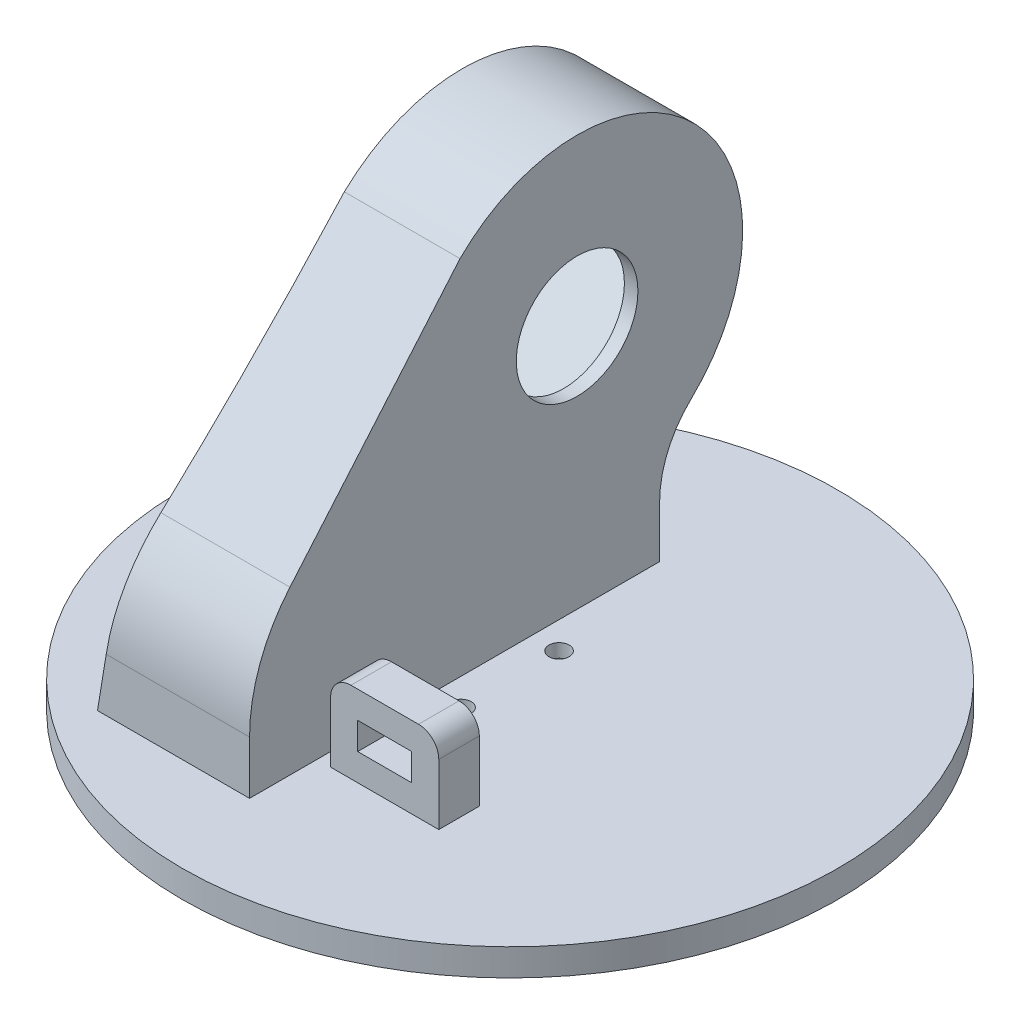
SolidWorks part; units mm, degrees
ref_plane "Front Plane" through (0, 0, 0) normal (0, 0, 1) x (1, 0, 0)
ref_plane "Top Plane" through (0, 0, 0) normal (0, 1, 0) x (1, 0, 0)
ref_plane "Right Plane" through (0, 0, 0) normal (1, 0, 0) x (0, 0, -1)
sketch "Sketch2" plane through (0, 0, 0) normal (0, 1, 0) x (1, 0, 0)
  circle A0 centre (0, 0) radius 48.5
  dimension "D1" = 97
extrude "Boss-Extrude1" add sketch "Sketch2" along normal blind 4
sketch "Sketch4" plane through (0, 0, 0) normal (0, -1, 0) x (1, 0, 0)
  circle A0 centre (0, 7.25) radius 1.5
  circle A1 centre (0, -7.25) radius 1.5
  dimension "D1" = 3
  dimension "D2" = 3
  dimension "D3" = 14.5
  dimension "D4" = 7.25
extrude "Cut-Extrude2" cut sketch "Sketch4" against normal through all
sketch "Sketch5" plane through (0, 0, 0) normal (0, -1, 0) x (1, 0, 0)
  circle A0 centre (0, 0) radius 3.75
  dimension "D1" = 7.5
extrude "Cut-Extrude3" cut sketch "Sketch5" against normal blind 1.5
ref_plane "Plane1" through (-4, 0, 0) normal (1, 0, 0) x (0, 0, -1)
sketch "Sketch7" plane through (-4, 0, 0) normal (1, 0, 0) x (0, 0, -1)
  line L0 (23.1299, 11.6445) -> (23.1299, 4)
  line L5 (48.5, 4) -> (-48.5, 4) construction
  line L6 (-27.2273, 29.5362) -> (-1.2843, 55.4793)
  line L7 (-43.5609, 4) -> (23.1299, 4)
  line L11 (-34.5496, 4) -> (-34.5496, 11.8586)
  arc A4 (28.7298, 24.692) -> (-1.2843, 55.4793) centre (13.9185, 40.2765) ccw
  arc A5 (28.7298, 24.692) -> (23.1299, 11.6445) centre (41.1299, 11.6445) ccw
  arc A6 (-27.2273, 29.5362) -> (-34.5496, 11.8586) centre (-9.5496, 11.8586) ccw
  dimension "D1" = 25
  dimension "D4" = 43
  dimension "D3" = 18
  dimension "D5" = 45
extrude "Boss-Extrude2" add sketch "Sketch7" against normal blind 14
ref_plane "Plane2" through (-6, 0, 0) normal (1, 0, 0) x (0, 0, -1)
sketch "Sketch8" plane through (-6, 0, 0) normal (1, 0, 0) x (0, 0, -1)
  line L0 (-27.2273, 29.5362) -> (-1.2843, 55.4793) construction
  line L1 (-15.2496, 25.9576) -> (13.7417, 54.9489)
  line L2 (-15.2496, 25.9576) -> (-0.4004, 11.1083)
  line L3 (-0.4004, 11.1083) -> (28.591, 40.0997)
  line L4 (13.7417, 54.9489) -> (28.591, 40.0997)
  line L5 (-15.2496, 25.9576) -> (28.591, 40.0997) construction
  line L6 (-0.4004, 11.1083) -> (13.7417, 54.9489) construction
  point P0 (6.6707, 33.0286)
  point P11 (13.9185, 40.2765)
  dimension "D1" = 41
  dimension "D2" = 21
  dimension "D3" = 90
  dimension "D4" = 20.5
  dimension "D5" = 90
  dimension "D6" = 10.25
  dimension "D7" = 10.5
extrude "Cut-Extrude5" cut sketch "Sketch8" against normal up to next
sketch "Sketch9" plane through (-18, 0, 0) normal (-1, 0, 0) x (0, 0, 1)
  line L0 (-13.7417, 54.9489) -> (-28.591, 40.0997) construction
  line L3 (-21.1664, 47.5243) -> (-22.536, 48.894) construction
  circle A0 centre (-20.1057, 53.5347) radius 1.3
  circle A1 centre (-27.1768, 46.4637) radius 1.3
  circle A2 centre (6.7644, 12.5225) radius 1.3
  circle A3 centre (13.8354, 19.5936) radius 1.3
  dimension "D1" = 2.6
  dimension "D5" = 5
  dimension "D6" = 90
  dimension "D2" = 3.5
  dimension "D3" = 2
  dimension "D4" = 2
extrude "Cut-Extrude6" cut sketch "Sketch9" against normal blind 7.5
sketch "Sketch11" plane through (-4, 0, 0) normal (1, 0, 0) x (0, 0, -1)
  circle A0 centre (13.9185, 40.2765) radius 9
  dimension "D1" = 18
extrude "Cut-Extrude9" cut sketch "Sketch11" against normal up to next
sketch "Sketch17" plane through (-18, 0, 0) normal (-1, 0, 0) x (0, 0, 1)
  line L0 (29.3486, 31.6576) -> (3.4056, 57.6006)
  line L1 (-26.1299, 11.6445) -> (-26.1299, 1)
  line L2 (-26.1299, 1) -> (37.5496, 1)
  line L3 (37.5496, 1) -> (37.5496, 11.8586)
  line L4 (27.2273, 29.5362) -> (1.2843, 55.4793)
  line L5 (-23.1299, 11.6445) -> (-23.1299, 4)
  line L6 (-23.1299, 4) -> (34.5496, 4)
  line L7 (34.5496, 4) -> (34.5496, 11.8586)
  line L9 (-23.1299, 11.6445) -> (-23.1299, 4)
  line L10 (-23.1299, 4) -> (34.5496, 4)
  line L11 (34.5496, 4) -> (34.5496, 11.8586)
  line L12 (-26.1299, 4) -> (37.5496, 4)
  line L13 (48.5, 4) -> (-48.5, 4) construction
  line L14 (3.4056, 57.6006) -> (28.5745, 28.0776)
  line L15 (1.2843, 55.4793) -> (26.295, 26.1272)
  line L16 (31.5496, 11.8586) -> (31.5496, 4)
  line L18 (27.2273, 29.5362) -> (1.2843, 55.4793) construction
  arc A0 (3.4056, 57.6006) -> (-30.7965, 22.5174) centre (-13.9185, 40.2765) ccw
  arc A1 (-26.1299, 11.6445) -> (-30.7965, 22.5174) centre (-41.1299, 11.6445) ccw
  arc A2 (37.5496, 11.8586) -> (29.3486, 31.6576) centre (9.5496, 11.8586) ccw
  arc A3 (1.2843, 55.4793) -> (-28.7298, 24.692) centre (-13.9185, 40.2765) ccw
  arc A4 (-23.1299, 11.6445) -> (-28.7298, 24.692) centre (-41.1299, 11.6445) ccw
  arc A5 (34.5496, 11.8586) -> (27.2273, 29.5362) centre (9.5496, 11.8586) ccw
  arc A6 (1.2843, 55.4793) -> (-28.7298, 24.692) centre (-13.9185, 40.2765) ccw
  arc A7 (-23.1299, 11.6445) -> (-28.7298, 24.692) centre (-41.1299, 11.6445) ccw
  arc A8 (34.5496, 11.8586) -> (27.2273, 29.5362) centre (9.5496, 11.8586) ccw
  arc A9 (31.5496, 11.8586) -> (25.106, 27.4149) centre (9.5496, 11.8586) ccw
  line M16 (27.2273, 29.5362) -> (1.2843, 55.4793)
  arc M17 (1.2843, 55.4793) -> (-28.7298, 24.692) centre (-13.9185, 40.2765) ccw
  arc M18 (-28.7298, 24.692) -> (-23.1299, 11.6445) centre (-41.1299, 11.6445) cw
  line M19 (-23.1299, 11.6445) -> (-23.1299, 4)
  line M21 (34.5496, 4) -> (34.5496, 11.8586)
  arc M22 (34.5496, 11.8586) -> (27.2273, 29.5362) centre (9.5496, 11.8586) ccw
  dimension "D1" = 0
  dimension "D2" = 3
  dimension "D3" = 3
extrude "Boss-Extrude7" add sketch "Sketch17" along normal blind 9 and the other way up to surface (14 mm away) contours A9 L16 L12 L15 M21 M22 M16 | A1 L1 L12 L14 A0 M19 M18 M17 M16 M22 other way up to face at (-4, 40.2765, -22.9185)
sketch "Sketch25" plane through (-18, 0, 0) normal (-1, 0, 0) x (0, 0, 1)
  line L0 (-23.1299, 11.6445) -> (-23.1299, 4)
  line L1 (48.5, 4) -> (-48.5, 4) construction
  line L2 (-23.1299, 11.6445) -> (-23.1299, 4) construction
  line L3 (1.2843, 55.4793) -> (26.295, 26.1272) construction
  line L4 (31.5496, 4) -> (-23.1299, 4) construction
  line L5 (31.5496, 11.8586) -> (31.5496, 4) construction
  line L6 (31.5496, 4) -> (-23.1299, 4)
  line L7 (31.5496, 11.8586) -> (31.5496, 4)
  line L8 (1.2843, 55.4793) -> (26.295, 26.1272)
  arc A0 (-23.1299, 11.6445) -> (-28.7298, 24.692) centre (-41.1299, 11.6445) ccw construction
  arc A1 (1.2843, 55.4793) -> (-28.7298, 24.692) centre (-13.9185, 40.2765) ccw construction
  arc A2 (-23.1299, 11.6445) -> (-28.7298, 24.692) centre (-41.1299, 11.6445) ccw
  arc A3 (31.5496, 11.8586) -> (26.295, 26.1272) centre (9.5496, 11.8586) ccw construction
  arc A4 (31.5496, 11.8586) -> (26.295, 26.1272) centre (9.5496, 11.8586) ccw
  spline S0 degree 3 poles (-28.7298, 24.692) (-21.9549, 18.2532) (-19.0941, 12.798) (-15.1299, 4) knots 0 0 0 0 1 1 1 1
  spline S1 degree 2 poles (11.7516, 43.195) (26.5513, 25.8264) (25.5496, 4) knots 0 0 0 1 1 1
  dimension "D2" = 8
  dimension "D1" = 6
extrude "Boss-Extrude10" add sketch "Sketch25" along normal up to surface (9 mm away) contours S0 L6 L0 A2 | A4 S1 A2 S0 L8 up to face at (-27, 22.2911, 0.3951)
sketch "Sketch26" plane through (0, 0, 0) normal (0, 0, 1) x (1, 0, 0)
  line L0 (-4, 64.7765) -> (-27, 64.7765) construction
  line L1 (-27, 4) -> (-4, 4) construction
  line L2 (-27, 4) -> (-27, 11.8586) construction
  line L3 (-26, 64.7765) -> (-27, 64.7765)
  line L4 (-27, 64.7765) -> (-27, 4)
  line L5 (-27, 4) -> (-23, 4)
  spline S0 degree 2 poles (-26, 64.7765) (-24.7724, 34.3751) (-23, 4) knots 0 0 0 1 1 1
  dimension "D1" = 1
  dimension "D2" = 4
  dimension "D3" = 2
extrude "Cut-Extrude15" [suppressed] cut sketch "Sketch26" against normal through all both and the other way through all contours L4 L5 S0 L3
sketch "Sketch27" plane through (0, 4, 0) normal (0, 1, 0) x (1, 0, 0)
  line L1 (-2, -18.5496) -> (14, -18.5496)
  line L2 (-2, -18.5496) -> (-2, -24.5496)
  line L3 (-2, -24.5496) -> (14, -24.5496)
  line L4 (14, -18.5496) -> (14, -24.5496)
  line L5 (-27, -34.5496) -> (-4, -34.5496) construction
  line L6 (-4, -34.5496) -> (-4, 26.1299) construction
  dimension "D1" = 10
  dimension "D2" = 6
  dimension "D3" = 16
  dimension "D4" = 2
extrude "Boss-Extrude11" add sketch "Sketch27" along normal blind 12
fillet "Fillet6" radius 3 2 edges at (14, 16, 21.5496) (-2, 16, 21.5496)
sketch "Sketch28" plane through (0, 0, 24.5496) normal (0, 0, 1) x (1, 0, 0)
  line L8 (10, 12) -> (2, 12)
  line L9 (2, 12) -> (2, 8)
  line L10 (2, 8) -> (10, 8)
  line L11 (10, 8) -> (10, 12)
  line L12 (10, 12) -> (2, 12)
  line L13 (2, 12) -> (2, 8)
  line L14 (2, 8) -> (10, 8)
  line L15 (10, 8) -> (10, 12)
  dimension "D1" = 4
extrude "Cut-Extrude16" cut sketch "Sketch28" against normal up to next
sketch "Sketch29" plane through (0, 0, 0) normal (0, 0, 1) x (1, 0, 0)
  line L0 (-4, 64.7765) -> (-27, 64.7765) construction
  line L1 (-27, 4) -> (-4, 4) construction
  line L2 (-21, 64.7765) -> (-27, 64.7765)
  line L3 (-27, 64.7765) -> (-27, 4)
  line L4 (-27, 4) -> (-26.5, 4)
  line L5 (48.5, 4) -> (-48.5, 4) construction
  spline S0 degree 2 poles (-21, 64.7765) (-21.2205, 34.1409) (-26.5, 4) knots 0 0 0 1 1 1
  dimension "D1" = 6
  dimension "D2" = 4
  dimension "D3" = 0.5
  dimension "D4" = 25
extrude "Cut-Extrude17" cut sketch "Sketch29" against normal through all both and the other way through all
sketch "Sketch30" plane through (0, 0, 0) normal (0, -1, 0) x (1, 0, 0)
  line L28 (-1.6213, 6.6238) -> (-2.453, 6.7518)
  line L29 (-2.453, 6.7518) -> (-4.8981, 8.2352)
  line L30 (-4.8981, 8.2352) -> (-13.8346, 11.8577)
  line L31 (-16.907, 6.7938) -> (-9.5665, 0.5407)
  line L32 (-9.5665, 0.5407) -> (-7.1215, -0.9428)
  line L33 (-7.1215, -0.9428) -> (-6.6238, -1.6213)
  line L34 (-6.6238, -1.6213) -> (-6.7518, -2.453)
  line L35 (-6.7518, -2.453) -> (-8.2352, -4.8981)
  line L36 (-8.2352, -4.8981) -> (-11.8577, -13.8346)
  line L37 (-6.7938, -16.907) -> (-0.5407, -9.5665)
  line L38 (-0.5407, -9.5665) -> (0.9428, -7.1215)
  line L39 (0.9428, -7.1215) -> (1.6213, -6.6238)
  line L40 (1.6213, -6.6238) -> (2.453, -6.7518)
  line L41 (2.453, -6.7518) -> (4.8981, -8.2352)
  line L42 (4.8981, -8.2352) -> (13.8346, -11.8577)
  line L43 (16.907, -6.7938) -> (9.5665, -0.5407)
  line L44 (9.5665, -0.5407) -> (7.1215, 0.9428)
  line L45 (7.1215, 0.9428) -> (6.6238, 1.6213)
  line L46 (6.6238, 1.6213) -> (6.7518, 2.453)
  line L47 (6.7518, 2.453) -> (8.2352, 4.8981)
  line L48 (8.2352, 4.8981) -> (11.8577, 13.8346)
  line L49 (6.7938, 16.907) -> (0.5407, 9.5665)
  line L50 (0.5407, 9.5665) -> (-0.9428, 7.1215)
  line L51 (-0.9428, 7.1215) -> (-1.6213, 6.6238)
  arc A12 (-13.8346, 11.8577) -> (-16.907, 6.7938) centre (-14.9616, 9.0775) ccw
  arc A13 (-11.8577, -13.8346) -> (-6.7938, -16.907) centre (-9.0775, -14.9616) ccw
  arc A14 (13.8346, -11.8577) -> (16.907, -6.7938) centre (14.9616, -9.0775) ccw
  arc A15 (11.8577, 13.8346) -> (6.7938, 16.907) centre (9.0775, 14.9616) ccw
extrude "Cut-Extrude19" cut sketch "Sketch30" against normal blind 2
